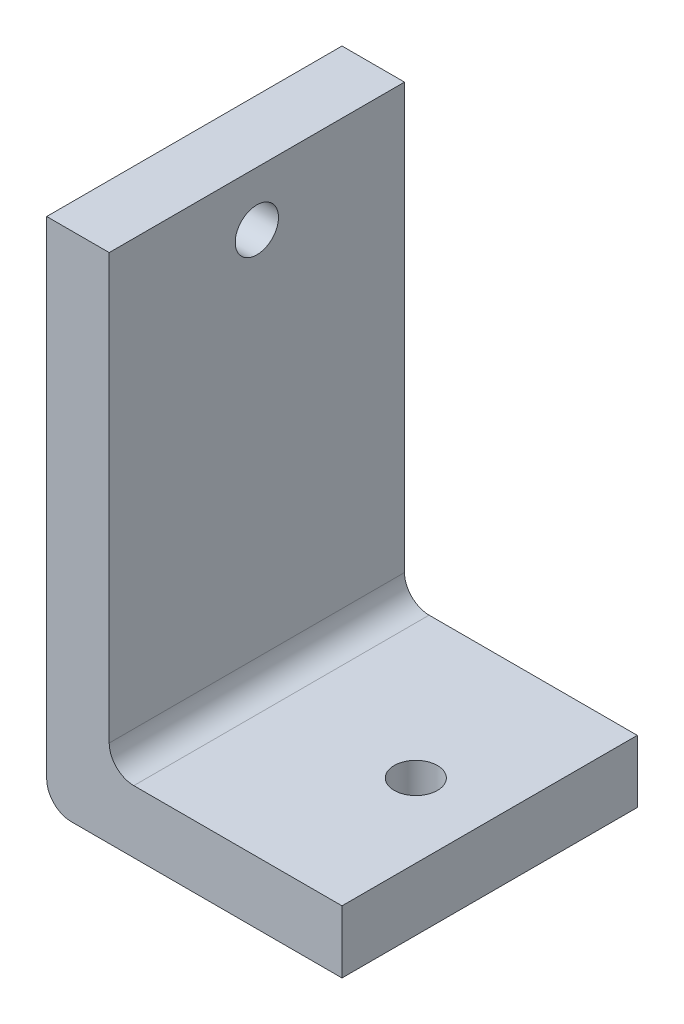
SolidWorks part; units mm, degrees
material "6061-T6 Al"
ref_plane "Front Plane" through (0, 0, 0) normal (0, 0, 1) x (1, 0, 0)
ref_plane "Top Plane" through (0, 0, 0) normal (0, 1, 0) x (1, 0, 0)
ref_plane "Right Plane" through (0, 0, 0) normal (1, 0, 0) x (0, 0, -1)
sketch "Sketch1" plane through (0, 0, 0) normal (0, 0, 1) x (1, 0, 0)
  line L0 (0, 0) -> (50.8, 0)
  line L1 (0, 0) -> (0, 55)
  dimension "D1" = 55
  dimension "D2" = 50.8
extrude "Extrude-Thin1" add sketch "Sketch1" against normal blind 240 thin thin type one direction wall 6.35
sketch "Sketch3" plane through (0, 6.35, 0) normal (0, 1, 0) x (1, 0, 0)
  line L0 (0, 240) -> (0, 0) construction
  line L1 (30, 245) -> (65, 245)
  line L2 (30, 245) -> (30, -55)
  line L3 (30, -55) -> (65, -55)
  line L4 (65, 245) -> (65, -55)
  line L5 (50.8, 240) -> (6.35, 240) construction
  dimension "D1" = 30
  dimension "D2" = 35
  dimension "D3" = 5
  dimension "D4" = 300
extrude "Extrude2" cut sketch "Sketch3" against normal through all
sketch "Sketch4" plane through (0, 6.35, 0) normal (0, 1, 0) x (1, 0, 0)
  line L0 (30, 240) -> (6.35, 240) construction
  line L1 (30, 240) -> (30, 0) construction
  line L2 (20.25, 172.25) -> (24.75, 172.25)
  line L3 (20.25, 167.75) -> (24.75, 167.75)
  line L4 (-3.0451, 120) -> (27.5098, 120) construction
  line L5 (20.25, 67.75) -> (24.75, 67.75)
  line L6 (20.25, 72.25) -> (24.75, 72.25)
  line L7 (30, 0) -> (6.35, 0) construction
  circle A0 centre (22.5, 170) radius 2.25 construction
  circle A1 centre (22.5, 70) radius 2.25 construction
  arc A2 (20.25, 172.25) -> (20.25, 167.75) centre (20.25, 170) ccw
  arc A3 (24.75, 167.75) -> (24.75, 172.25) centre (24.75, 170) ccw
  arc A4 (20.25, 67.75) -> (20.25, 72.25) centre (20.25, 70) cw
  arc A5 (24.75, 72.25) -> (24.75, 67.75) centre (24.75, 70) cw
  circle A6 centre (22.5, 170) radius 2 construction
  dimension "D3" = 4.5
  dimension "D7" = 4
  dimension "D8" = 2.5
  dimension "D9" = 3
  dimension "D1" = 100
  dimension "D2" = 70
  dimension "D4" = 7.5
  dimension "D5" = 4.5
  dimension "D6" = 2.25
  dimension "D10" = 70
sketch "Sketch7" plane through (6.35, 0, 0) normal (1, 0, 0) x (0, 0, -1)
  line L0 (240, 0) -> (0, 0) construction
  line L1 (-5, 82) -> (295, 82)
  line L2 (-5, 82) -> (-5, 52)
  line L3 (-5, 52) -> (295, 52)
  line L4 (295, 82) -> (295, 52)
  line L5 (0, 6.35) -> (0, 55) construction
  dimension "D1" = 52
  dimension "D2" = 30
  dimension "D3" = 5
  dimension "D4" = 300
extrude "Extrude4" cut sketch "Sketch7" against normal through all
sketch "Sketch10" plane through (6.35, 0, 0) normal (1, 0, 0) x (0, 0, -1)
  line L0 (0, 6.35) -> (0, 52) construction
  line L1 (30, 67) -> (210, 67)
  line L2 (30, 67) -> (30, 22)
  line L3 (35, 17) -> (205, 17)
  line L4 (210, 67) -> (210, 22)
  line L6 (0, 52) -> (240, 52) construction
  line L7 (240, 0) -> (0, 0) construction
  line L8 (240, 6.35) -> (240, 52) construction
  arc A0 (35, 17) -> (30, 22) centre (35, 22) cw
  arc A1 (210, 22) -> (205, 17) centre (205, 22) cw
  dimension "D6" = 5
  dimension "D1" = 30
  dimension "D2" = 30
  dimension "D3" = 35
  dimension "D4" = 50
  dimension "D5" = 17
extrude "Extrude5" cut sketch "Sketch10" against normal through all
sketch "Sketch11" plane through (6.35, 0, 0) normal (1, 0, 0) x (0, 0, -1)
  line L0 (0, 6.35) -> (0, 52) construction
  line L1 (240, 6.35) -> (240, 52) construction
  line L2 (0, 52) -> (30, 52) construction
  line L3 (120, 61.8909) -> (120, -15.2982) construction
  line L4 (17.25, 48.75) -> (12.75, 48.75)
  line L5 (12.75, 44.25) -> (17.25, 44.25)
  line L6 (222.75, 48.75) -> (227.25, 48.75)
  line L7 (227.25, 44.25) -> (222.75, 44.25)
  circle A0 centre (225, 46.5) radius 2.25 construction
  circle A1 centre (15, 46.5) radius 2.25 construction
  arc A2 (12.75, 48.75) -> (12.75, 44.25) centre (12.75, 46.5) ccw
  arc A3 (17.25, 44.25) -> (17.25, 48.75) centre (17.25, 46.5) ccw
  arc A4 (227.25, 48.75) -> (227.25, 44.25) centre (227.25, 46.5) cw
  arc A5 (222.75, 44.25) -> (222.75, 48.75) centre (222.75, 46.5) cw
  dimension "D1" = 4.5
  dimension "D7" = 4.5
  dimension "D2" = 15
  dimension "D3" = 15
  dimension "D4" = 5.5
  dimension "D5" = 2.25
  dimension "D6" = 2.25
hole_wizard "Tapped Hole for #8-32 Helicoil1" positions "3DSketch3" profile "Sketch32" tap size "#8-32" standard "Helicoil® Inch" end condition through all
sketch3d "3DSketch3"
  point P0 (6.35, 46.5, -15)
  point P3 (6.35, 46.5, -225)
sketch "Sketch32" plane through (6.35, 46.5, -15) normal (0, 1, 0) x (0, 0, -1)
  line L0 (0, 0) -> (0, 6.35)
  line L1 (0, 6.35) -> (2.1971, 6.35)
  line L2 (2.1971, 6.35) -> (2.1971, 0)
  line L5 (2.1971, 0) -> (0, 0)
  line L11 (0, -6.35) -> (0, 107.95) construction
  dimension "Thru Tap Drill Dia." = 4.3942
  dimension "Thru Tap Drill Depth" = 6.35
cosmetic thread "Hole Thread2" parameters "D1"=6.35, "D2"=5.2756
cosmetic thread "Hole Thread3" parameters "D1"=6.35, "D2"=5.2756
sketch "Sketch14" plane through (0, 6.35, 0) normal (0, 1, 0) x (1, 0, 0)
  circle A0 centre (22.5, 70) radius 2.25 construction
  circle A1 centre (22.5, 170) radius 2.25 construction
  circle A2 centre (22.5, 70) radius 2.25
  circle A3 centre (22.5, 170) radius 2.25
sketch "Sketch26" plane through (6.35, 0, 0) normal (1, 0, 0) x (0, 0, -1)
  line L0 (0, 52) -> (30, 52) construction
  line L1 (-10, 62) -> (210, 62)
  line L2 (-10, 62) -> (-10, -8)
  line L3 (-10, -8) -> (210, -8)
  line L4 (210, 62) -> (210, -8)
  line L6 (0, 6.35) -> (0, 52) construction
  line L7 (210, 22) -> (210, 52) construction
  dimension "D1" = 10
  dimension "D2" = 70
  dimension "D3" = 10
extrude "Extrude18" cut sketch "Sketch26" along normal through all and the other way through all
sketch "Sketch27" plane through (0, 6.35, 0) normal (0, 1, 0) x (1, 0, 0)
  line L0 (30, 240) -> (30, 210) construction
  line L1 (30, 240) -> (6.35, 240) construction
  circle A0 centre (22.5, 225) radius 2.25
  dimension "D1" = 4.5
  dimension "D2" = 7.5
  dimension "D3" = 15
hole_wizard "Tapped Hole for #8-32 Helicoil2" positions "3DSketch5" profile "Sketch34" tap size "#8-32" standard "Helicoil® Inch" end condition through all
sketch3d "3DSketch5"
  point P0 (22.5, 6.35, -225)
cosmetic thread "Hole Thread1" parameters "D1"=6.35, "D2"=5.2756
sketch "Sketch34" plane through (22.5, 6.35, -225) normal (1, 0, 0) x (0, 0, 1)
  line L0 (0, 0) -> (0, 6.35)
  line L1 (0, 6.35) -> (2.1971, 6.35)
  line L2 (2.1971, 6.35) -> (2.1971, 0)
  line L5 (2.1971, 0) -> (0, 0)
  line L11 (0, -6.35) -> (0, 107.95) construction
  dimension "Thru Tap Drill Dia." = 4.3942
  dimension "Thru Tap Drill Depth" = 6.35
fillet "Fillet1" radius 2.5 2 edges at (0, 0, -225) (6.35, 6.35, -225)
